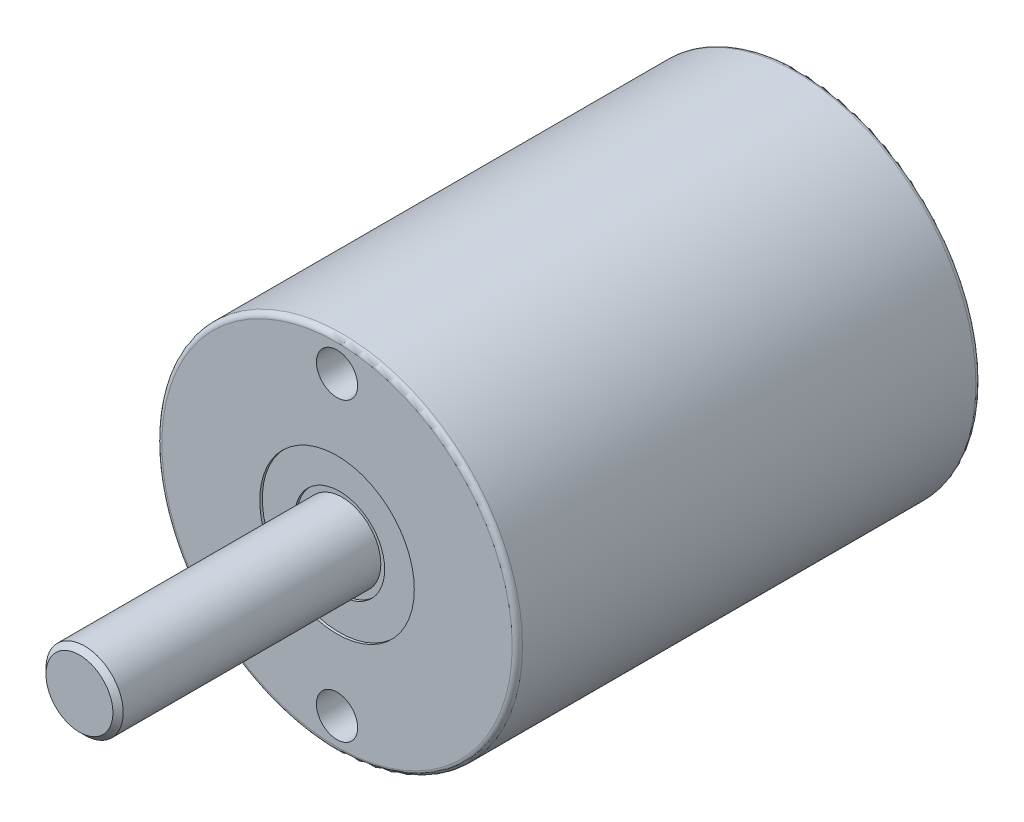
SolidWorks part; units mm, degrees
ref_plane "前视基准面" through (0, 0, 0) normal (0, 0, 1) x (1, 0, 0)
ref_plane "上视基准面" through (0, 0, 0) normal (0, 1, 0) x (1, 0, 0)
ref_plane "右视基准面" through (0, 0, 0) normal (1, 0, 0) x (0, 0, -1)
sketch "草图1" plane through (0, 0, 0) normal (0, 0, 1) x (1, 0, 0)
  circle A0 centre (0, 0) radius 7
  dimension "D1" = 14
extrude "凸台-拉伸1" add sketch "草图1" along normal blind 18
fillet "圆角1" radius 0.2 2 edges at (7, 0, 18) (7, 0, 0)
sketch "草图2" plane through (0, 0, 18) normal (0, 0, 1) x (1, 0, 0)
  circle A0 centre (0, 0) radius 1.5
  dimension "D1" = 3
extrude "凸台-拉伸2" add sketch "草图2" along normal blind 10
chamfer "倒角1" distance 0.2 angle 45 1 edges at (1.5, 0, 28)
sketch "草图3" plane through (0, 0, 18) normal (0, 0, 1) x (1, 0, 0)
  line L0 (0, 5.75) -> (0, -5.75) construction
  circle A0 centre (0, 0) radius 5.75 construction
  dimension "D1" = 11.5
hole_wizard "M2 螺纹孔1" positions "3D草图1" profile "草图5" tap size "M2" standard "GB"
sketch3d "3D草图1"
  point P0 (0, 5.75, 18)
  point P3 (0, -5.75, 18)
sketch "草图5" plane through (0, 5.75, 18) normal (1, 0, 0) x (0, -1, 0)
  line L0 (0, 0) -> (0, 6.4807)
  line L1 (0, 6.4807) -> (0.8, 6)
  line L2 (0.8, 6) -> (0.8, 0)
  line L5 (0.8, 0) -> (0, 0)
  line L10 (0, 6.4807) -> (-0.8, 6) construction
  line L11 (0, -6.35) -> (0, 107.95) construction
  dimension "螺纹孔钻头直径" = 1.6
  dimension "螺纹孔钻头深度" = 6
  dimension "导头角度" = 118
cosmetic thread "孔螺蚊线1" parameters "D1"=4, "D2"=2
cosmetic thread "孔螺蚊线2" parameters "D1"=4, "D2"=2
sketch "草图6" plane through (0, 0, 18) normal (0, 0, 1) x (1, 0, 0)
  circle A0 centre (0, 0) radius 1.5 construction
  circle A1 centre (0, 0) radius 1.5
  circle A2 centre (0, 0) radius 1.75
  dimension "D1" = 3.5
extrude "切除-拉伸1" cut sketch "草图6" against normal blind 0.2
sketch "草图7" plane through (0, 0, 18) normal (0, 0, 1) x (1, 0, 0)
  circle A0 centre (0, 0) radius 3
  circle A1 centre (0, 0) radius 1.75 construction
  circle A2 centre (0, 0) radius 1.75
  dimension "D1" = 6
extrude "切除-拉伸2" cut sketch "草图7" against normal blind 0.1
